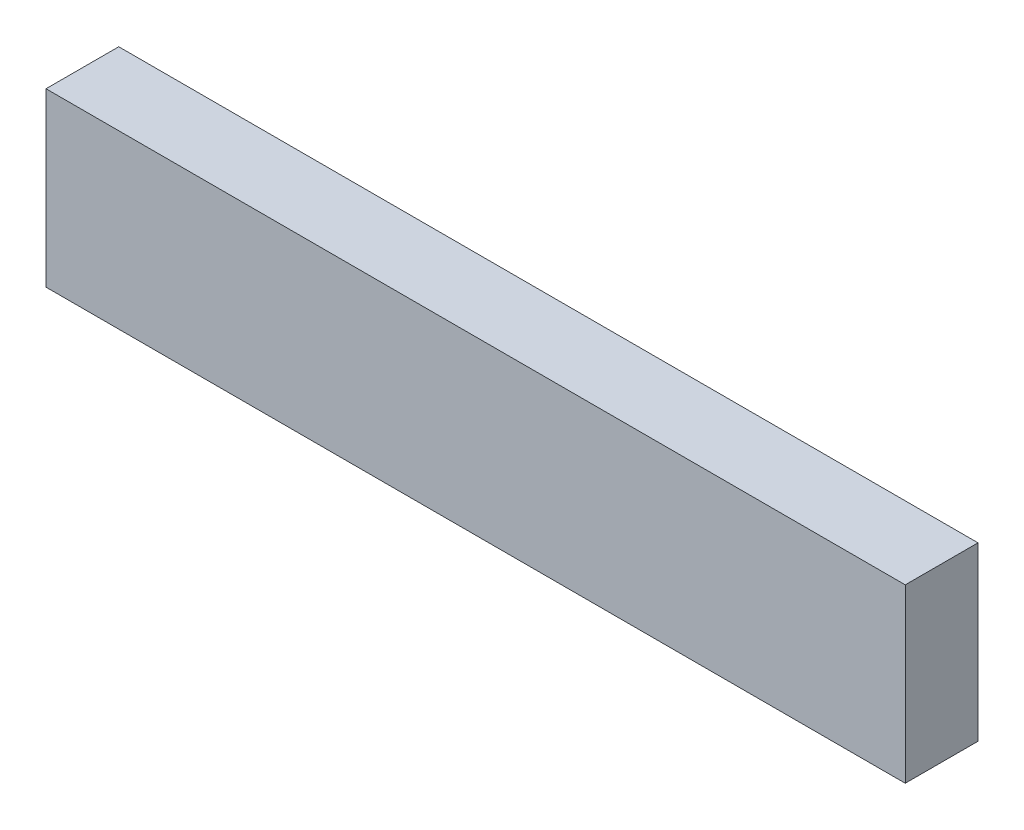
SolidWorks part; units mm, degrees
ref_plane "Front Plane" through (0, 0, 0) normal (0, 0, 1) x (1, 0, 0)
ref_plane "Top Plane" through (0, 0, 0) normal (0, 1, 0) x (1, 0, 0)
ref_plane "Right Plane" through (0, 0, 0) normal (1, 0, 0) x (0, 0, -1)
sketch "Sketch1" plane through (0, 0, 0) normal (0, 0, 1) x (1, 0, 0)
  line L1 (0, 0) -> (75, 0)
  line L2 (0, 0) -> (0, 15)
  line L3 (0, 15) -> (75, 15)
  line L4 (75, 0) -> (75, 15)
  dimension "D1" = 75
  dimension "D2" = 15
extrude "Boss-Extrude1" add sketch "Sketch1" along normal blind 6.35
